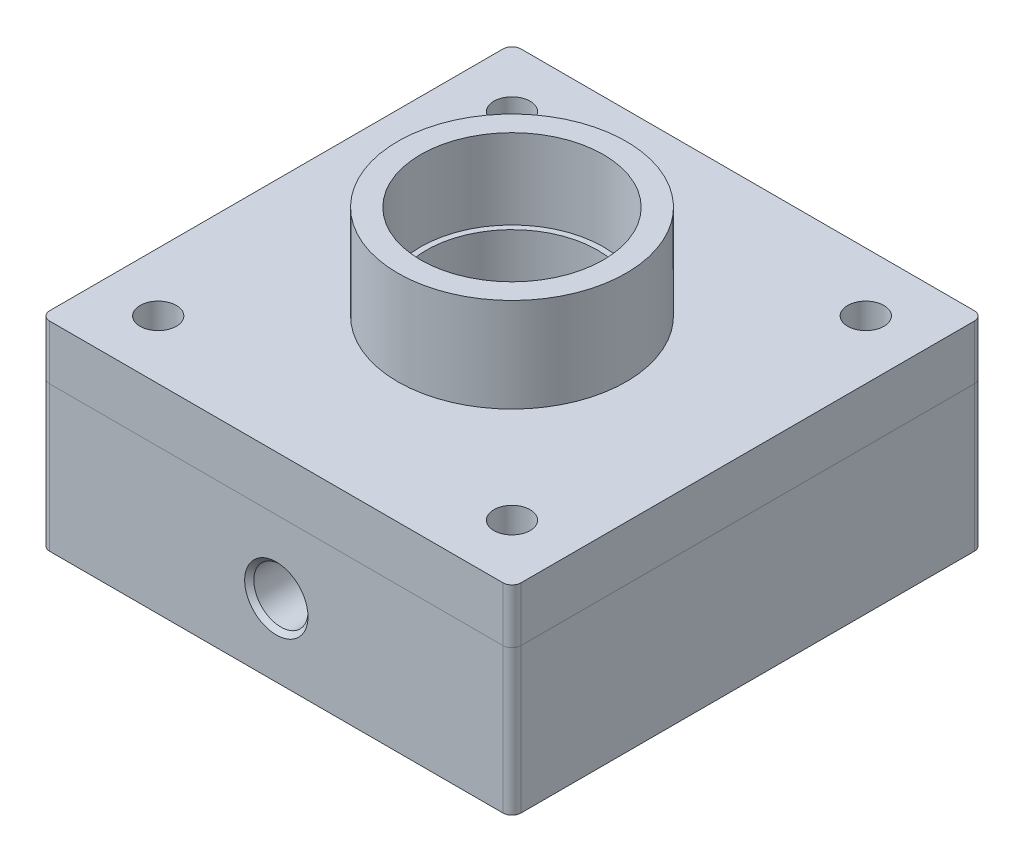
SolidWorks part; units mm, degrees
ref_plane "Front Plane" through (0, 0, 0) normal (0, 0, 1) x (1, 0, 0)
ref_plane "Top Plane" through (0, 0, 0) normal (0, 1, 0) x (1, 0, 0)
ref_plane "Right Plane" through (0, 0, 0) normal (1, 0, 0) x (0, 0, -1)
sketch "Sketch1" plane through (0, 0, 0) normal (0, 1, 0) x (1, 0, 0)
  line L1 (-82.55, -82.55) -> (82.55, -82.55)
  line L2 (-82.55, -82.55) -> (-82.55, 82.55)
  line L3 (-82.55, 82.55) -> (82.55, 82.55)
  line L4 (82.55, -82.55) -> (82.55, 82.55)
  line L5 (-82.55, -82.55) -> (82.55, 82.55) construction
  line L6 (-82.55, 82.55) -> (82.55, -82.55) construction
  point P0 (0, 0)
  dimension "D1" = 165.1
extrude "Boss-Extrude1" add sketch "Sketch1" along normal blind 50.8
sketch "Sketch2" plane through (0, 50.8, 0) normal (0, 1, 0) x (1, 0, 0)
  circle A0 centre (0, 0) radius 40
  dimension "D1" = 80
extrude "Boss-Extrude2" add sketch "Sketch2" along normal blind 52
sketch "Sketch3" plane through (0, 102.8, 0) normal (0, 1, 0) x (1, 0, 0)
  circle A0 centre (0, 0) radius 32
  dimension "D1" = 64
extrude "Cut-Extrude1" cut sketch "Sketch3" against normal blind 28
sketch "Sketch4" plane through (0, 74.8, 0) normal (0, 1, 0) x (1, 0, 0)
  circle A0 centre (0, 0) radius 30
  dimension "D1" = 60
extrude "Cut-Extrude2" cut sketch "Sketch4" against normal blind 22
fillet "Fillet1" radius 3.175 4 edges at (-82.55, 25.4, 82.55) (-82.55, 25.4, -82.55) (82.55, 25.4, -82.55) (82.55, 25.4, 82.55)
sketch "Sketch5" plane through (0, 0, 0) normal (0, -1, 0) x (1, 0, 0)
  circle A0 centre (0, 0) radius 20
  dimension "D1" = 40
extrude "Cut-Extrude3" cut sketch "Sketch5" against normal blind 40
sketch "Sketch6" plane through (0, 0, 0) normal (0, -1, 0) x (1, 0, 0)
  circle A0 centre (0, 0) radius 69.85
  circle A1 centre (0, 0) radius 76.2
  dimension "D1" = 152.4
  dimension "D2" = 139.7
extrude "Cut-Extrude4" cut sketch "Sketch6" against normal blind 8
sketch "Sketch7" plane through (0, 0, 82.55) normal (0, 0, 1) x (1, 0, 0)
  line L0 (-79.375, 25.4) -> (79.375, 25.4) construction
  line L1 (-79.375, 50.8) -> (-79.375, 0) construction
  line L2 (79.375, 0) -> (79.375, 50.8) construction
hole_wizard "1/2-14 NPSM Tapped Hole1" positions "Sketch8" profile "Sketch9" tap size "1/2-14 NPSM" standard "ANSI Inch"
sketch "Sketch8" plane through (0, 0, 82.55) normal (0, 0, 1) x (1, 0, 0)
  line L0 (-79.375, 25.4) -> (79.375, 25.4) construction
  point P0 (0, 25.4)
sketch "Sketch9" plane through (0, 25.4, 82.55) normal (1, 0, 0) x (0, -1, 0)
  line L0 (0, 0) -> (0, 52.9403)
  line L1 (0, 52.9403) -> (9.4869, 47.24)
  line L2 (9.4869, 47.24) -> (9.4869, 1.6002)
  line L3 (9.4869, 1.6002) -> (11.0871, 0)
  line L5 (11.0871, 0) -> (0, 0)
  line L6 (-9.4869, 1.6002) -> (-11.0871, 0) construction
  line L10 (0, 52.9403) -> (-9.4869, 47.24) construction
  line L11 (0, -6.35) -> (0, 107.95) construction
  dimension "Tap Drill Dia." = 18.9738
  dimension "Tap Drill Depth" = 47.24
  dimension "Near C'Sink Dia." = 22.1742
  dimension "Near C'Sink Angle" = 90
  dimension "Drill Angle" = 118
cosmetic thread "Hole Thread1" parameters "D1"=41.91, "D2"=20.9042
sketch "Sketch10" plane through (0, 0, 0) normal (0, -1, 0) x (1, 0, 0)
  line L0 (-79.375, 82.55) -> (79.375, 82.55) construction
  circle A0 centre (0, 50.55) radius 6.35
  dimension "D1" = 12.7
  dimension "D2" = 32
extrude "Cut-Extrude5" cut sketch "Sketch10" against normal blind 25 contours A0
sketch "Sketch11" plane through (0, 0, 0) normal (0, -1, 0) x (1, 0, 0)
  line L1 (-61.9638, -61.9638) -> (61.9638, -61.9638) construction
  line L2 (-61.9638, -61.9638) -> (-61.9638, 61.9638) construction
  line L3 (-61.9638, 61.9638) -> (61.9638, 61.9638) construction
  line L4 (61.9638, -61.9638) -> (61.9638, 61.9638) construction
  line L5 (-61.9638, -61.9638) -> (61.9638, 61.9638) construction
  line L6 (-61.9638, 61.9638) -> (61.9638, -61.9638) construction
  circle A0 centre (0, 0) radius 87.63 construction
  circle A1 centre (-61.9638, 61.9638) radius 6.35
  circle A2 centre (61.9638, 61.9638) radius 6.35
  circle A3 centre (61.9638, -61.9638) radius 6.35
  circle A4 centre (-61.9638, -61.9638) radius 6.35
  dimension "D1" = 175.26
  dimension "D2" = 12.7
extrude "Cut-Extrude6" cut sketch "Sketch11" against normal through all
sketch "Sketch12" plane through (0, 50.8, 0) normal (0, 1, 0) x (1, 0, 0)
  line L4 (-82.55, 79.375) -> (-82.55, -79.375)
  line L5 (-79.375, -82.55) -> (79.375, -82.55)
  line L6 (82.55, -79.375) -> (82.55, 79.375)
  line L7 (79.375, 82.55) -> (-79.375, 82.55)
  line L8 (-82.55, 79.375) -> (-82.55, -79.375)
  line L9 (-79.375, -82.55) -> (79.375, -82.55)
  line L10 (82.55, -79.375) -> (82.55, 79.375)
  line L11 (79.375, 82.55) -> (-79.375, 82.55)
  circle A0 centre (0, 0) radius 40 construction
  circle A1 centre (61.9638, 61.9638) radius 6.35 construction
  circle A2 centre (61.9638, -61.9638) radius 6.35 construction
  circle A3 centre (-61.9638, -61.9638) radius 6.35 construction
  circle A4 centre (0, 0) radius 40
  circle A5 centre (61.9638, 61.9638) radius 6.35
  circle A6 centre (61.9638, -61.9638) radius 6.35
  circle A7 centre (-61.9638, -61.9638) radius 6.35
  circle A8 centre (-61.9638, 61.9638) radius 6.35 construction
  circle A9 centre (-61.9638, 61.9638) radius 6.35
  arc A14 (-82.55, -79.375) -> (-79.375, -82.55) centre (-79.375, -79.375) ccw
  arc A15 (79.375, -82.55) -> (82.55, -79.375) centre (79.375, -79.375) ccw
  arc A16 (82.55, 79.375) -> (79.375, 82.55) centre (79.375, 79.375) ccw
  arc A17 (-79.375, 82.55) -> (-82.55, 79.375) centre (-79.375, 79.375) ccw
  arc A18 (-82.55, -79.375) -> (-79.375, -82.55) centre (-79.375, -79.375) ccw
  arc A19 (79.375, -82.55) -> (82.55, -79.375) centre (79.375, -79.375) ccw
  arc A20 (82.55, 79.375) -> (79.375, 82.55) centre (79.375, 79.375) ccw
  arc A21 (-79.375, 82.55) -> (-82.55, 79.375) centre (-79.375, 79.375) ccw
  dimension "D1" = 0
extrude "Boss-Extrude3" add sketch "Sketch12" along normal blind 19.05 separate body
